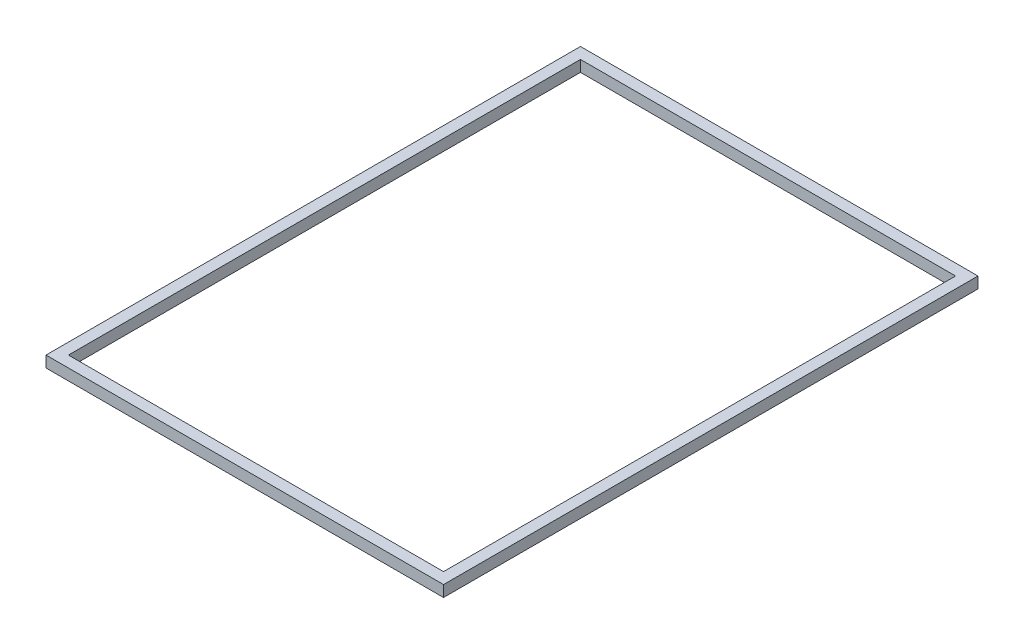
SolidWorks part; units mm, degrees
material "Ductile Iron (SN)"
ref_plane "Front Plane" through (0, 0, 0) normal (0, 0, 1) x (1, 0, 0)
ref_plane "Top Plane" through (0, 0, 0) normal (0, 1, 0) x (1, 0, 0)
ref_plane "Right Plane" through (0, 0, 0) normal (1, 0, 0) x (0, 0, -1)
sketch "Sketch1" plane through (0, 0, 0) normal (0, 1, 0) x (1, 0, 0)
  line L1 (-450, 605) -> (450, 605)
  line L2 (-450, 605) -> (-450, -605)
  line L3 (-450, -605) -> (450, -605)
  line L4 (450, 605) -> (450, -605)
  line L5 (-450, 605) -> (450, -605) construction
  line L6 (-450, -605) -> (450, 605) construction
  point P0 (0, 0)
  dimension "D1" = 900
  dimension "D2" = 1210
sketch "Sketch2" plane through (0, 0, 0) normal (1, 0, 0) x (0, 0, -1)
  line L0 (-603.8, 24.2) -> (-580.8, 24.2)
  line L1 (-605, 0) -> (-579.6, 0)
  line L2 (-605, 0) -> (-605, 25.4)
  line L3 (-605, 25.4) -> (-579.6, 25.4)
  line L4 (-579.6, 0) -> (-579.6, 25.4)
  line L5 (-580.8, 1.2) -> (-580.8, 24.2)
  line L6 (-603.8, 1.2) -> (-580.8, 1.2)
  line L7 (-603.8, 1.2) -> (-603.8, 24.2)
  point P4 (0, 0)
  dimension "D1" = 25.4
  dimension "D2" = 1.2
sweep "Sweep1" add profiles "Sketch2" path "Sketch1"
